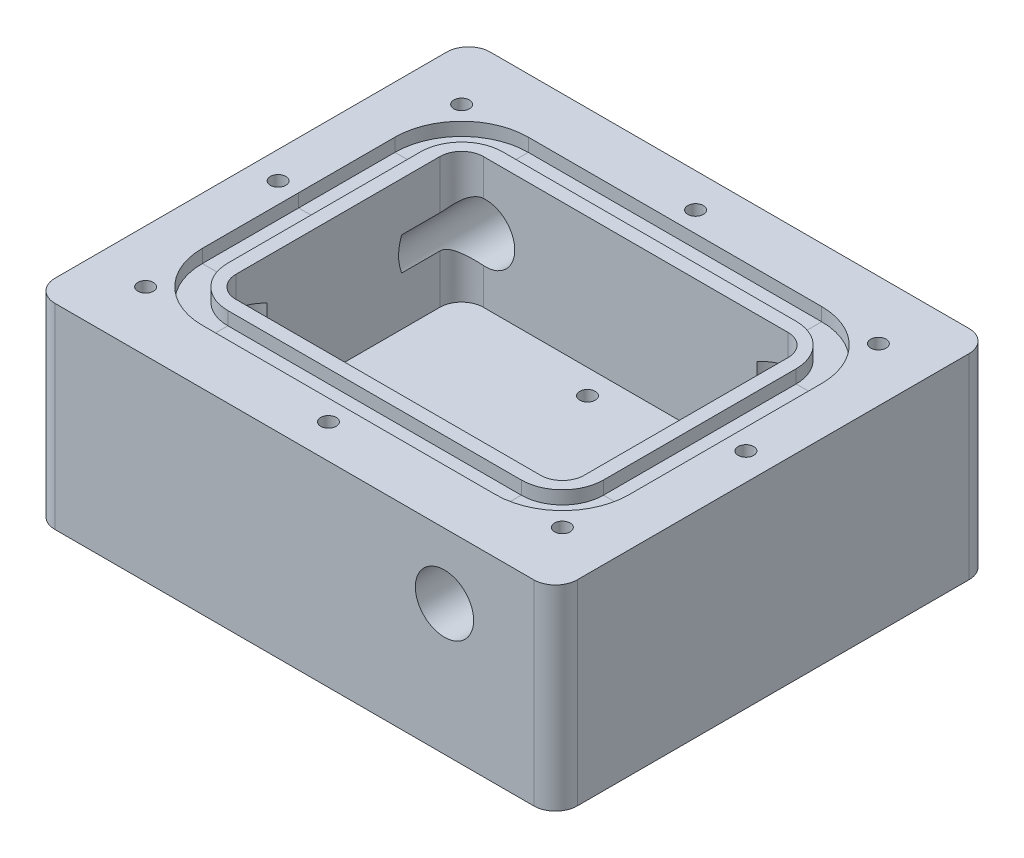
SolidWorks part; units mm, degrees
ref_plane "Front Plane" through (0, 0, 0) normal (0, 0, 1) x (1, 0, 0)
ref_plane "Top Plane" through (0, 0, 0) normal (0, 1, 0) x (1, 0, 0)
ref_plane "Right Plane" through (0, 0, 0) normal (1, 0, 0) x (0, 0, -1)
sketch "Sketch1" plane through (0, 0, 0) normal (0, 1, 0) x (1, 0, 0)
  line L1 (-38.1, 31.75) -> (38.1, 31.75)
  line L2 (-38.1, 31.75) -> (-38.1, -31.75)
  line L3 (-38.1, -31.75) -> (38.1, -31.75)
  line L4 (38.1, 31.75) -> (38.1, -31.75)
  line L5 (-38.1, 31.75) -> (38.1, -31.75) construction
  line L6 (-38.1, -31.75) -> (38.1, 31.75) construction
  point P0 (0, 0)
  dimension "D1" = 63.5
  dimension "D2" = 76.2
extrude "Boss-Extrude1" add sketch "Sketch1" along normal mid plane 28.575
sketch "Sketch2" plane through (0, 14.2875, 0) normal (0, 1, 0) x (1, 0, 0)
  line L0 (-25.4, 0) -> (-38.1, 0) construction
  line L1 (-25.4, 18.05) -> (25.4, 18.05)
  line L2 (-25.4, 18.05) -> (-25.4, -18.05)
  line L3 (-25.4, -18.05) -> (25.4, -18.05)
  line L4 (25.4, 18.05) -> (25.4, -18.05)
  line L5 (-25.4, 18.05) -> (25.4, -18.05) construction
  line L6 (-25.4, -18.05) -> (25.4, 18.05) construction
  line L7 (-38.1, 31.75) -> (-38.1, -31.75) construction
  line L8 (0, 18.05) -> (0, 31.75) construction
  line L9 (38.1, 31.75) -> (-38.1, 31.75) construction
  point P0 (0, 0)
  dimension "D1" = 12.7
  dimension "D2" = 13.7
extrude "Cut-Extrude1" cut sketch "Sketch2" against normal blind 15.875
sketch "Sketch3" plane through (0, -1.5875, 0) normal (0, 1, 0) x (1, 0, 0)
  line L0 (25.4, 18.05) -> (14.4, 18.05) construction
  line L1 (-25.4, -18.05) -> (-14.4, -18.05) construction
  line L2 (-25.4, -18.05) -> (-25.4, -7.05) construction
  line L3 (-25.4, -7.05) -> (-14.4, -7.05)
  line L4 (-14.4, -18.05) -> (-14.4, -7.05)
  line L5 (25.4, 18.05) -> (14.4, 18.05) construction
  line L6 (25.4, 18.05) -> (25.4, 7.05) construction
  line L7 (25.4, 7.05) -> (14.4, 7.05)
  line L8 (14.4, 18.05) -> (14.4, 7.05)
  line L9 (25.4, 7.05) -> (25.4, 18.05) construction
  line L10 (-25.4, -18.05) -> (-14.4, -18.05) construction
  line L11 (-25.4, -7.05) -> (-25.4, -18.05) construction
  line L12 (25.4, -18.05) -> (25.4, 18.05)
  line L13 (25.4, 18.05) -> (-25.4, 18.05)
  line L14 (-25.4, 18.05) -> (-25.4, -18.05)
  line L15 (-25.4, -18.05) -> (25.4, -18.05)
  line L16 (25.4, -18.05) -> (25.4, 7.05)
  line L17 (14.4, 18.05) -> (-25.4, 18.05)
  line L18 (-25.4, 18.05) -> (-25.4, -7.05)
  line L19 (-14.4, -18.05) -> (25.4, -18.05)
  dimension "D1" = 11
  dimension "D2" = 0
extrude "Cut-Extrude2" cut sketch "Sketch3" against normal blind 3.175
fillet "Fillet1" radius 3.175 10 edges at (25.4, 4.7625, 18.05) (-14.4, -3.175, 18.05) (-14.4, -3.175, 7.05) (-25.4, -3.175, 7.05) (-25.4, 4.7625, -18.05) (25.4, -3.175, -7.05) (14.4, -3.175, -18.05) (14.4, -3.175, -7.05) (-25.4, 6.35, 18.05) (25.4, 6.35, -18.05)
sketch "Sketch5" plane through (0, -14.2875, 0) normal (0, -1, 0) x (1, 0, 0)
  line L0 (25.4, -3.875) -> (25.4, -14.875) construction
  line L1 (22.225, -18.05) -> (11.225, -18.05) construction
  line L2 (14.4, -14.875) -> (14.4, -10.225) construction
  line L3 (17.575, -7.05) -> (22.225, -7.05) construction
  line L4 (-25.4, 3.875) -> (-25.4, 14.875) construction
  line L5 (-22.225, 18.05) -> (-11.225, 18.05) construction
  line L6 (-14.4, 14.875) -> (-14.4, 10.225) construction
  line L7 (-17.575, 7.05) -> (-22.225, 7.05) construction
  line L8 (25.4, -3.875) -> (25.4, -14.875) construction
  line L9 (22.225, -18.05) -> (11.225, -18.05) construction
  line L10 (14.4, -14.875) -> (14.4, -10.225) construction
  line L11 (17.575, -7.05) -> (22.225, -7.05) construction
  line L12 (-25.4, 3.875) -> (-25.4, 14.875) construction
  line L13 (-22.225, 18.05) -> (-11.225, 18.05) construction
  line L14 (-14.4, 14.875) -> (-14.4, 10.225) construction
  line L15 (-17.575, 7.05) -> (-22.225, 7.05) construction
  line L16 (-22.4, 7.05) -> (-22.4, 15.05) construction
  line L17 (-22.4, 15.05) -> (-14.4, 15.05) construction
  line L18 (22.4, -7.05) -> (22.4, -15.05) construction
  line L19 (22.4, -15.05) -> (14.4, -15.05) construction
  arc A0 (22.225, -18.05) -> (25.4, -14.875) centre (22.225, -14.875) ccw construction
  arc A1 (11.225, -18.05) -> (14.4, -14.875) centre (11.225, -14.875) ccw construction
  arc A2 (17.575, -7.05) -> (14.4, -10.225) centre (17.575, -10.225) ccw construction
  arc A3 (22.225, -7.05) -> (25.4, -3.875) centre (22.225, -3.875) ccw construction
  arc A4 (-22.225, 18.05) -> (-25.4, 14.875) centre (-22.225, 14.875) ccw construction
  arc A5 (-11.225, 18.05) -> (-14.4, 14.875) centre (-11.225, 14.875) ccw construction
  arc A6 (-17.575, 7.05) -> (-14.4, 10.225) centre (-17.575, 10.225) ccw construction
  arc A7 (-22.225, 7.05) -> (-25.4, 3.875) centre (-22.225, 3.875) ccw construction
  arc A8 (22.225, -18.05) -> (25.4, -14.875) centre (22.225, -14.875) ccw construction
  arc A9 (11.225, -18.05) -> (14.4, -14.875) centre (11.225, -14.875) ccw construction
  arc A10 (17.575, -7.05) -> (14.4, -10.225) centre (17.575, -10.225) ccw construction
  arc A11 (22.225, -7.05) -> (25.4, -3.875) centre (22.225, -3.875) ccw construction
  arc A12 (-22.225, 18.05) -> (-25.4, 14.875) centre (-22.225, 14.875) ccw construction
  arc A13 (-11.225, 18.05) -> (-14.4, 14.875) centre (-11.225, 14.875) ccw construction
  arc A14 (-17.575, 7.05) -> (-14.4, 10.225) centre (-17.575, 10.225) ccw construction
  arc A15 (-22.225, 7.05) -> (-25.4, 3.875) centre (-22.225, 3.875) ccw construction
  point P31 (-22.4, 15.05)
  point P32 (22.4, -15.05)
  dimension "D1" = 8
sketch "Sketch7" plane through (0, -4.7625, 0) normal (0, 1, 0) x (1, 0, 0)
  line L0 (0, 0) -> (-0.2785, 0) construction
  line L1 (-14.1215, 17.7715) -> (-0.2785, 17.7715) construction
  line L2 (-14.1215, 17.7715) -> (-14.1215, -15.5025) construction
  line L3 (-14.1215, -15.5025) -> (-0.2785, -15.5025) construction
  line L4 (-0.2785, 17.7715) -> (-0.2785, -15.5025) construction
  line L5 (-14.1215, -15.5025) -> (-14.4, -15.5025) construction
  line L6 (-14.4, -14.875) -> (-14.4, -10.225) construction
  line L7 (-7.2, 17.7715) -> (-7.2, 18.05) construction
  line L8 (11.225, 18.05) -> (-22.225, 18.05) construction
  line L9 (0, 0) -> (0, -18.05) construction
  line L10 (-22.225, -18.05) -> (22.225, -18.05) construction
  line L11 (-3.4535, 17.7715) -> (-3.4535, 14.4695) construction
  line L12 (-3.4535, 14.4695) -> (-0.2785, 14.4695) construction
  line L13 (-10.9465, -15.5025) -> (-10.9465, -11.6905) construction
  line L14 (-10.9465, -11.6905) -> (-14.1215, -11.6905) construction
  line L15 (7.2, 15.5025) -> (7.2, 18.05) construction
  line L16 (0.2785, -17.7715) -> (14.1215, -17.7715) construction
  line L17 (0.2785, -17.7715) -> (0.2785, 15.5025) construction
  line L18 (0.2785, 15.5025) -> (14.1215, 15.5025) construction
  line L19 (14.1215, -17.7715) -> (14.1215, 15.5025) construction
  line L20 (14.1215, 15.5025) -> (14.4, 15.5025) construction
  line L21 (14.4, 14.875) -> (14.4, 10.225) construction
  line L22 (-7.2, -15.5025) -> (-7.2, -18.05) construction
  line L23 (0.2785, -14.4695) -> (3.4535, -14.4695) construction
  line L24 (3.4535, -14.4695) -> (3.4535, -17.7715) construction
  line L25 (10.9465, 15.5025) -> (10.9465, 11.6905) construction
  line L26 (10.9465, 11.6905) -> (14.1215, 11.6905) construction
  point P21 (-3.4535, 14.4695)
  point P25 (-10.9465, -11.6905)
  point P43 (10.9465, 11.6905)
  point P44 (3.4535, -14.4695)
  dimension "D1" = 13.843
  dimension "D2" = 33.274
  dimension "D3" = 3.175
  dimension "D4" = 3.302
  dimension "D5" = 26.16
hole_wizard "#4-40 Tapped Hole1" positions "3DSketch1" profile "Sketch8" tap size "#4-40" standard "ANSI Inch"
sketch3d "3DSketch1"
  point P0 (10.9465, -4.7625, -11.6905)
  point P3 (3.4535, -4.7625, 14.4695)
  point P6 (-3.4535, -4.7625, -14.4695)
  point P9 (-10.9465, -4.7625, 11.6905)
sketch "Sketch8" plane through (10.9465, -4.7625, -11.6905) normal (1, 0, 0) x (0, 0, 1)
  line L0 (0, 0) -> (0, 4)
  line L1 (0, 4) -> (1.1303, 3.3208)
  line L2 (1.1303, 3.3208) -> (1.1303, 0)
  line L5 (1.1303, 0) -> (0, 0)
  line L10 (0, 4) -> (-1.1303, 3.3208) construction
  line L11 (0, -6.35) -> (0, 107.95) construction
  dimension "Tap Drill Dia." = 2.2606
  dimension "Tap Drill Depth" = 4
  dimension "Drill Angle" = 118
cosmetic thread "Hole Thread1" parameters "D1"=5.69, "D2"=2.8448
cosmetic thread "Hole Thread2" parameters "D1"=5.69, "D2"=2.8448
cosmetic thread "Hole Thread3" parameters "D1"=5.69, "D2"=2.8448
cosmetic thread "Hole Thread4" parameters "D1"=5.69, "D2"=2.8448
hole_wizard "1/4 NPT Tapped Hole1" positions "3DSketch2" profile "Sketch9" size "1/4" standard "ANSI Inch"
sketch3d "3DSketch2"
  point P0 (-22.225, -14.2875, 14.875)
  point P3 (22.4, -14.2875, -15.05)
sketch "Sketch9" plane through (-22.225, -14.2875, 14.875) normal (1, 0, 0) x (0, 0, -1)
  line L0 (0, 0) -> (0, 26)
  line L1 (5.5626, 22.6577) -> (0, 26)
  line L2 (-5.5626, 22.6577) -> (0, 26) construction
  line L3 (5.5626, 22.6577) -> (5.5626, 10.02)
  line L4 (5.5626, 10.02) -> (5.9437, 10.02)
  line L5 (5.9437, 10.02) -> (6.2437, 0)
  line L6 (-5.9437, 10.02) -> (-6.2437, 0) construction
  line L7 (6.2437, 0) -> (0, 0)
  line L8 (0, -6.35) -> (0, 107.95) construction
  line L11 (-5.5626, 10.02) -> (-5.9437, 10.02) construction
  dimension "Tap Drill Dia." = 11.1252
  dimension "Tap Drill Depth" = 26
  dimension "Thread Dia." = 12.4874
  dimension "Thread Angle" = 3.43
  dimension "Thread Depth" = 10.02
  dimension "Drill Angle" = 118
cosmetic thread "Hole Thread5" parameters "D1"=10.02, "D2"=13.716
cosmetic thread "Hole Thread6" parameters "D1"=10.02, "D2"=13.716
sketch "Sketch10" plane through (0, 0, -31.75) normal (0, 0, -1) x (-1, 0, 0)
  line L0 (25.4, -4.7625) -> (25.4, 14.2875) construction
  line L1 (25.4, -4.7625) -> (25.4, 14.2875) construction
  line L2 (25.4, 4.7625) -> (21.9, 4.7625) construction
  point P5 (21.9, 4.7625)
  dimension "D1" = 3.5
sketch "Sketch12" plane through (0, 0, 31.75) normal (0, 0, 1) x (1, 0, 0)
  line L0 (-25.4, 4.7625) -> (-21.9, 4.7625) construction
  line L1 (-25.4, 4.7625) -> (-21.9, 4.7625) construction
  line L2 (25.4, -4.7625) -> (25.4, 14.2875) construction
  line L3 (25.4, -4.7625) -> (25.4, 14.2875) construction
  line L4 (25.4, 4.7625) -> (21.9, 4.7625) construction
  point P7 (21.9, 4.7625)
hole_wizard "M10x1.5 Tapped Hole1" positions "3DSketch3" profile "Sketch11" tap size "M10x1.5" standard "ANSI Metric"
sketch3d "3DSketch3"
  point P0 (-21.9, 4.7625, -31.75)
  point P4 (21.9, 4.7625, 31.75)
sketch "Sketch11" plane through (-21.9, 4.7625, -31.75) normal (1, 0, 0) x (0, 1, 0)
  line L0 (0, 0) -> (0, 25)
  line L1 (0, 25) -> (4.25, 22.4463)
  line L2 (4.25, 22.4463) -> (4.25, 0)
  line L5 (4.25, 0) -> (0, 0)
  line L10 (0, 25) -> (-4.25, 22.4463) construction
  line L11 (0, -6.35) -> (0, 107.95) construction
  dimension "Tap Drill Dia." = 8.5
  dimension "Tap Drill Depth" = 25
  dimension "Drill Angle" = 118
cosmetic thread "Hole Thread7" parameters "D1"=20, "D2"=10
cosmetic thread "Hole Thread8" parameters "D1"=20, "D2"=10
sketch "Sketch14" plane through (0, 14.2875, 0) normal (0, 1, 0) x (1, 0, 0)
  line L0 (0, 18.05) -> (0, 20.05) construction
  line L1 (-21.4, 20.05) -> (21.4, 20.05)
  line L2 (-27.4, 14.05) -> (-27.4, -14.05)
  line L3 (-21.4, -20.05) -> (21.4, -20.05)
  line L4 (27.4, 14.05) -> (27.4, -14.05)
  line L5 (22.225, 18.05) -> (-22.225, 18.05) construction
  line L6 (-27.4, 0) -> (-25.4, 0) construction
  line L7 (-25.4, 14.875) -> (-25.4, -14.875) construction
  line L8 (0, -20.05) -> (0, -18.05) construction
  line L9 (-22.225, -18.05) -> (22.225, -18.05) construction
  line L10 (25.4, 0) -> (27.4, 0) construction
  line L11 (25.4, -14.875) -> (25.4, 14.875) construction
  line L12 (-25.4, 14.875) -> (-25.4, -3.875) construction
  arc A0 (21.4, -20.05) -> (27.4, -14.05) centre (21.4, -14.05) ccw
  arc A1 (27.4, 14.05) -> (21.4, 20.05) centre (21.4, 14.05) ccw
  arc A2 (-21.4, -20.05) -> (-27.4, -14.05) centre (-21.4, -14.05) cw
  arc A3 (-21.4, 20.05) -> (-27.4, 14.05) centre (-21.4, 14.05) ccw
  point P24 (27.4, 20.05)
  point P27 (-27.4, -20.05)
  point P30 (-27.4, 20.05)
  dimension "RingPathRadius" = 6
  dimension "RingInnerLength" = 54.8
  dimension "RingInnerWidth" = 40.1
  dimension "ORingExtrusionGap" = 2
sketch "Sketch16" plane through (0, 0, 0) normal (0, 0, 1) x (1, 0, 0)
  line L1 (-27.4, 14.2875) -> (-31.1242, 14.2875)
  line L2 (-27.4, 14.2875) -> (-27.4, 12.3635)
  line L3 (-27.4, 12.3635) -> (-31.1242, 12.3635)
  line L4 (-31.1242, 14.2875) -> (-31.1242, 12.3635)
  dimension "GlandDepth" = 1.9241
  dimension "GlandWidth" = 3.7242
sweep "Cut-Sweep1" cut profiles "Sketch16" path "Sketch14"
fillet "Fillet2" radius 3.175 4 edges at (38.1, 0, 31.75) (-38.1, 0, 31.75) (-38.1, 0, -31.75) (38.1, 0, -31.75)
sketch "Sketch18" plane through (0, 14.2875, 0) normal (0, 1, 0) x (1, 0, 0)
  line L35 (-21.4, 26.7742) -> (-21.4, 23.7742) construction
  line L36 (-21.4, 26.7742) -> (-21.4, 31.75) construction
  line L37 (34.925, 31.75) -> (-34.925, 31.75) construction
  line L38 (-21.4, -23.7742) -> (-21.4, -26.7742) construction
  line L39 (-34.1242, 0) -> (-38.1, 0) construction
  line L40 (-38.1, 28.575) -> (-38.1, -28.575) construction
  line L41 (-34.1242, 0) -> (-31.1242, 0) construction
  line L42 (-31.1242, 0) -> (31.1242, 0) construction
  line L43 (31.1242, 14.05) -> (31.1242, -14.05) construction
  line L44 (31.1242, 0) -> (34.1242, 0) construction
  line L45 (34.1242, -14.05) -> (34.1242, 14.55) construction
  line L46 (-21.4, -26.7742) -> (21.4, -26.7742) construction
  line L47 (-34.1242, 0) -> (-34.1242, -14.05) construction
  line L48 (-34.1242, 14.05) -> (-34.1242, 0) construction
  line L49 (21.4098, 26.7742) -> (-21.4, 26.7742) construction
  line L50 (34.1242, 0) -> (38.1, 0) construction
  line L51 (38.1, -28.575) -> (38.1, 28.575) construction
  line L52 (-31.1242, -14.05) -> (-31.1242, 0) construction
  arc A30 (34.1242, 14.55) -> (21.4098, 26.7742) centre (21.4098, 14.05) ccw construction
  arc A31 (21.4, -26.7742) -> (34.1242, -14.05) centre (21.4, -14.05) ccw construction
  arc A32 (-34.1242, -14.05) -> (-21.4, -26.7742) centre (-21.4, -14.05) ccw construction
  arc A33 (-21.4, 26.7742) -> (-34.1242, 14.05) centre (-21.4, 14.05) ccw construction
  point P13 (30.2287, 23.2225)
  point P17 (-30.3974, 23.0474)
  point P18 (30.3974, -23.0474)
  point P19 (-30.3974, -23.0474)
  point P20 (0, -26.7742)
  point P22 (-34.1242, 0)
  point P89 (0.0049, 26.7742)
  point P94 (34.1242, 0)
  dimension "D1" = 3
hole_wizard "#4-40 Tapped Hole2" positions "Sketch18" profile "Sketch19" tap size "#4-40" standard "ANSI Inch"
sketch "Sketch19" plane through (34.1242, 14.2875, 0) normal (1, 0, 0) x (0, 0, 1)
  line L0 (0, 0) -> (0, 7.6)
  line L1 (0, 7.6) -> (1.1303, 6.9208)
  line L2 (1.1303, 6.9208) -> (1.1303, 0)
  line L5 (1.1303, 0) -> (0, 0)
  line L10 (0, 7.6) -> (-1.1303, 6.9208) construction
  line L11 (0, -6.35) -> (0, 107.95) construction
  dimension "Tap Drill Dia." = 2.2606
  dimension "Tap Drill Depth" = 7.6
  dimension "Drill Angle" = 118
cosmetic thread "Hole Thread9" parameters "D1"=5.69, "D2"=2.8448
cosmetic thread "Hole Thread10" parameters "D1"=5.69, "D2"=2.8448
cosmetic thread "Hole Thread11" parameters "D1"=5.69, "D2"=2.8448
cosmetic thread "Hole Thread12" parameters "D1"=5.69, "D2"=2.8448
cosmetic thread "Hole Thread13" parameters "D1"=5.69, "D2"=2.8448
cosmetic thread "Hole Thread14" parameters "D1"=5.69, "D2"=2.8448
cosmetic thread "Hole Thread15" parameters "D1"=5.69, "D2"=2.8448
cosmetic thread "Hole Thread16" parameters "D1"=5.69, "D2"=2.8448
equation "\"InnerRingWidth\"= 40.1'mm"
equation "\"InnerRingLength\"= 54.8'mm"
equation "\"RingPathRadius\"= 6'mm"
equation "\"RingPathLength\"= 2 * \"InnerRingLength\" + 2 * \"InnerRingWidth\" - ( 8 - 2 * 3.1415 ) * \"RingPathRadius\"'mm"
equation "\"RingStretch\"= .03"
equation "\"RingNomInnerDiameter\"= \"RingPathLength\" / 3.1415 / ( 1 + \"RingStretch\" ) / 25.4'Inches"
equation "\"RingInnerLength@Sketch14\"= \"InnerRingLength\""
equation "\"RingInnerWidth@Sketch14\"= \"InnerRingWidth\""
equation "\"RingPathRadius@Sketch14\"= \"RingPathRadius\""
equation "\"RingCompression\"= .25"
equation "\"RingCrossSectionHeight\"= .101'In"
equation "\"GlandDepth\"= \"RingCrossSectionHeight\" * ( 1 - \"RingCompression\" )'In"
equation "\"CrossSectionArea\"= .00833'In^2"
equation "\"GlandWidth\"= \"CrossSectionArea\" / \"GlandDepth\" / ( \"GlandFill\" )'In"
equation "\"GlandFill\"= .75"
equation "\"GlandWidth@Sketch16\"= \"GlandWidth\" * 25.4"
equation "\"GlandDepth@Sketch16\"= \"GlandDepth\" * 25.4"
